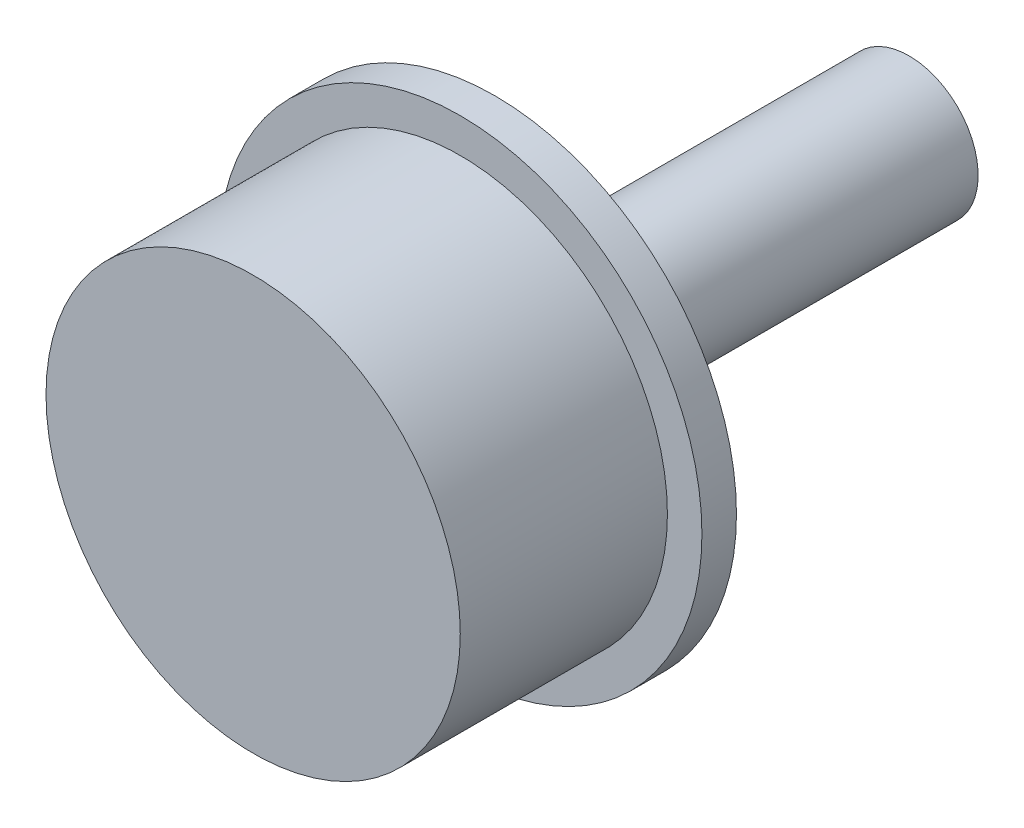
SolidWorks part; units mm, degrees
material "Unlegierter Baustahl"
ref_plane "Ebene vorne" through (0, 0, 0) normal (0, 0, 1) x (1, 0, 0)
ref_plane "Ebene oben" through (0, 0, 0) normal (0, 1, 0) x (1, 0, 0)
ref_plane "Ebene rechts" through (0, 0, 0) normal (1, 0, 0) x (0, 0, -1)
sketch "Skizze1" plane through (0, 0, 0) normal (1, 0, 0) x (0, 0, -1)
  line L0 (0, 0) -> (-32.0536, 0) construction
  line L1 (4, 1) -> (4, 0)
  line L5 (4, 0) -> (-4, 0)
  line L6 (-4, 0) -> (-3, 1)
  line L8 (-3, 1) -> (4, 1)
  dimension "D1" = 8
  dimension "D2" = 45
  dimension "D6" = 2
revolve "Rotation1" add sketch "Skizze1" angle 360 about L0
sketch "Skizze2" plane through (0, 0, 0) normal (1, 0, 0) x (0, 0, -1)
  line L2 (-2.5, 3) -> (-5.5, 3)
  line L3 (-5.5, 3) -> (-5.5, 0)
  line L4 (-5.5, 0) -> (-2, 0)
  line L5 (-2, 0) -> (0, 0) construction
  line L6 (-2.5, 3) -> (-2.5, 3.5)
  line L7 (-2.5, 3.5) -> (-2, 3.5)
  line L8 (-2, 3.5) -> (-2, 0)
  line L9 (4, -1) -> (4, 1) construction
  dimension "D1" = 3
  dimension "D2" = 7
  dimension "D3" = 6
  dimension "D4" = 0.5
  dimension "D5" = 6
revolve "Rotation2" add sketch "Skizze2" angle 360 about L5
